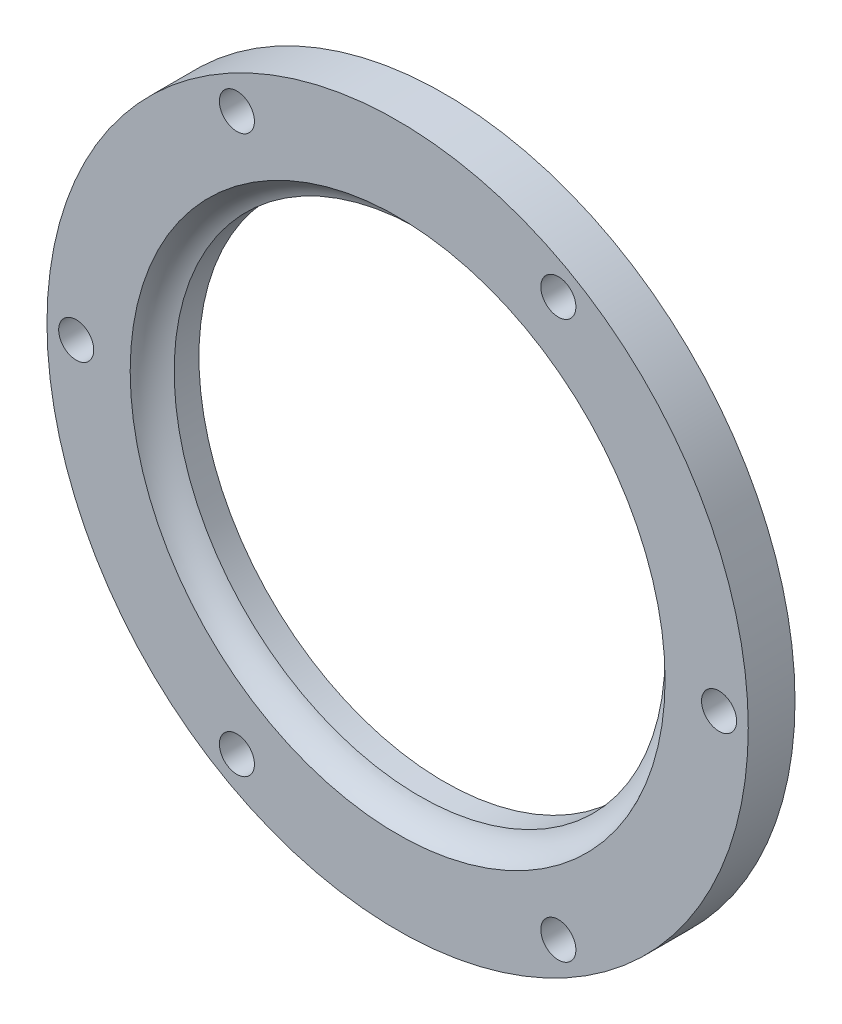
SolidWorks part; units mm, degrees
ref_plane "Piano frontale" through (0, 0, 0) normal (0, 0, 1) x (1, 0, 0)
ref_plane "Piano superiore" through (0, 0, 0) normal (0, 1, 0) x (1, 0, 0)
ref_plane "Piano destro" through (0, 0, 0) normal (1, 0, 0) x (0, 0, -1)
sketch "Schizzo1" plane through (0, 0, 0) normal (0, 0, 1) x (1, 0, 0)
  circle A0 centre (0, 0) radius 30
  circle A1 centre (0, 0) radius 21
  dimension "D1" = 60
  dimension "D2" = 42
extrude "Estrusione-Estrusione1" add sketch "Schizzo1" along normal blind 4
ref_axis "Assi1" through (0, 0, 4) along (0, 0, -1)
sketch "Schizzo2" plane through (0, 0, 0) normal (1, 0, 0) x (0, 0, -1)
  line L1 (0, -30) -> (0, 30) construction
  circle A0 centre (-5, 20) radius 3.05
  dimension "D1" = 6.1
  dimension "D2" = 20
  dimension "D3" = 5
revolve "Taglia-Rivoluzione1" cut sketch "Schizzo2" angle 360 about axis through (0, 0, 4) along (0, 0, -1)
sketch "Schizzo3" plane through (0, 0, 0) normal (0, 0, 1) x (1, 0, 0)
  circle A0 centre (0, 0) radius 27.5 construction
  circle A1 centre (-27.5, 0) radius 1.5
  dimension "D1" = 55
  dimension "D2" = 3
extrude "Taglio-Estrusione1" cut sketch "Schizzo3" along normal blind 10
sketch "Schizzo5" plane through (0, 0, 0) normal (0, 0, -1) x (-1, 0, 0)
  line L1 (24.75, -1.5877) -> (27.5, -3.1754)
  line L2 (27.5, -3.1754) -> (30.25, -1.5877)
  line L3 (30.25, -1.5877) -> (30.25, 1.5877)
  line L4 (30.25, 1.5877) -> (27.5, 3.1754)
  line L5 (27.5, 3.1754) -> (24.75, 1.5877)
  line L6 (24.75, 1.5877) -> (24.75, -1.5877)
  circle A0 centre (27.5, 0) radius 2.75 construction
  dimension "D1" = 5.5
pattern_circular "RipetizioneCircolare1" count 6 over 360 about axis through (0, 0, 0) along (0, 0, 1) of "Taglio-Estrusione1"
